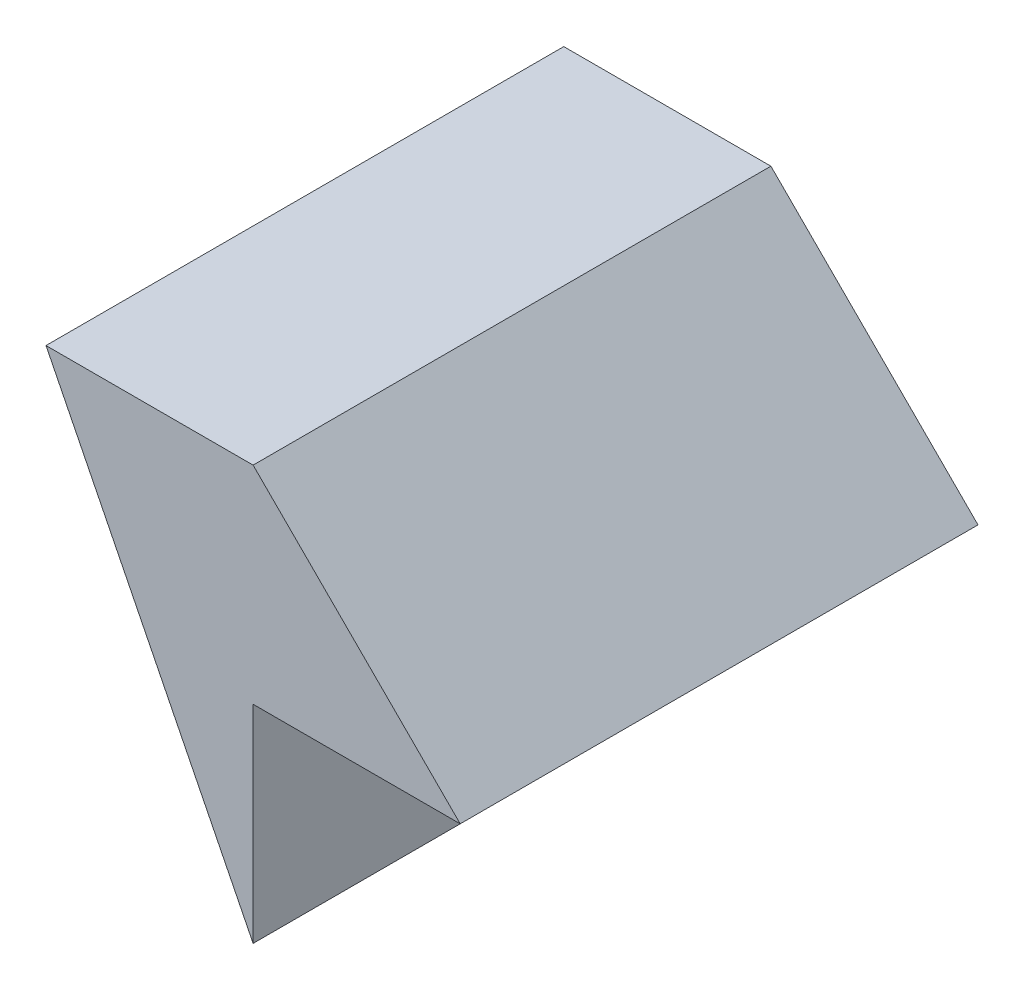
SolidWorks part; units mm, degrees
ref_plane "Front Plane" through (0, 0, 0) normal (0, 0, 1) x (1, 0, 0)
ref_plane "Top Plane" through (0, 0, 0) normal (0, 1, 0) x (1, 0, 0)
ref_plane "Right Plane" through (0, 0, 0) normal (1, 0, 0) x (0, 0, -1)
sketch "Sketch1" plane through (0, 0, 0) normal (0, 0, 1) x (1, 0, 0)
  line L0 (-10, 10) -> (0, 10)
  line L1 (0, 10) -> (10, 0)
  line L2 (10, 0) -> (0, 0)
  line L3 (0, 0) -> (0, -10)
  line L4 (0, -10) -> (-10, 10)
  point P4 (-10, -10)
  dimension "D1" = 10
  dimension "D2" = 10
  dimension "D3" = 10
  dimension "D4" = 10
  dimension "D5" = 10
  dimension "D6" = 20
  dimension "D7" = 20
extrude "Boss-Extrude1" add sketch "Sketch1" along normal blind 25
